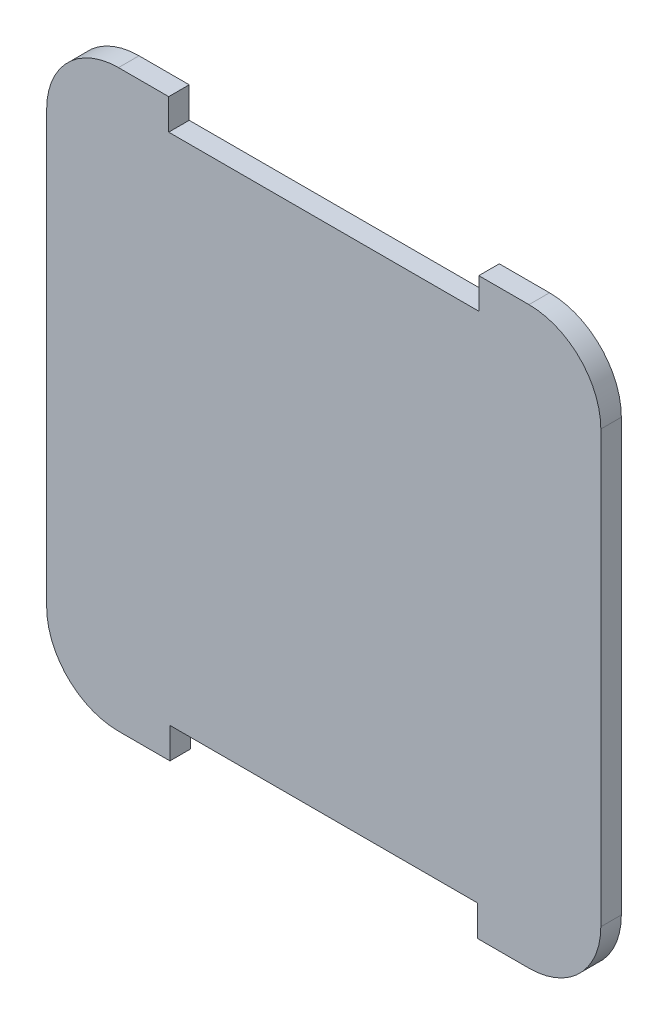
SolidWorks part; units mm, degrees
ref_plane "Front Plane" through (0, 0, 0) normal (0, 0, 1) x (1, 0, 0)
ref_plane "Top Plane" through (0, 0, 0) normal (0, 1, 0) x (1, 0, 0)
ref_plane "Right Plane" through (0, 0, 0) normal (1, 0, 0) x (0, 0, -1)
sketch "Sketch1" plane through (0, 0, 0) normal (0, 0, 1) x (1, 0, 0)
  line L2 (-13.5, 10.5) -> (-13.5, -10.5) construction
  line L5 (-13.5, 10.5) -> (-13.5, -10.5)
  line L6 (-10, 14) -> (10, 14)
  line L8 (-10, -14) -> (10, -14)
  line L9 (13.5, 10.5) -> (13.5, -10.5) construction
  line L10 (13.5, 10.5) -> (13.5, -10.5)
  arc A3 (-10, 14) -> (-13.5, 10.5) centre (-10, 10.5) ccw construction
  arc A7 (-10, 14) -> (-13.5, 10.5) centre (-10, 10.5) ccw
  arc A8 (10, -14) -> (13.5, -10.5) centre (10, -10.5) ccw construction
  arc A9 (-13.5, -10.5) -> (-10, -14) centre (-10, -10.5) ccw construction
  arc A10 (10, -14) -> (13.5, -10.5) centre (10, -10.5) ccw
  arc A11 (-13.5, -10.5) -> (-10, -14) centre (-10, -10.5) ccw
  arc A12 (13.5, 10.5) -> (10, 14) centre (10, 10.5) ccw construction
  arc A13 (13.5, 10.5) -> (10, 14) centre (10, 10.5) ccw
extrude "Boss-Extrude1" add sketch "Sketch1" along normal blind 1
sketch "Sketch2" plane through (0, 0, 1) normal (0, 0, 1) x (1, 0, 0)
  line L0 (10, 14) -> (-10, 14) construction
  line L1 (7.5538, 14) -> (-7.5538, 14)
  line L2 (7.2538, 12.5) -> (-7.2538, 12.5) construction
  line L3 (7.5538, 12.5) -> (-7.5538, 12.5)
  line L4 (-7.5538, 14) -> (-7.5538, 12.5) construction
  line L5 (-7.5538, 14) -> (-7.5538, 12.5)
  line L6 (7.5538, 12.5) -> (7.5538, 14) construction
  line L7 (7.5538, 12.5) -> (7.5538, 14)
  line L12 (-10, -14) -> (10, -14) construction
  line L13 (-7.4932, -14) -> (7.4932, -14)
  line L15 (-7.4964, -12.5) -> (7.4964, -12.5)
  line L16 (-7.4932, -14) -> (-7.4966, -12.446) construction
  line L17 (-7.4932, -14) -> (-7.4964, -12.5)
  line L18 (7.4932, -14) -> (7.4966, -12.446) construction
  line L19 (7.4932, -14) -> (7.4964, -12.5)
extrude "Cut-Extrude1" cut sketch "Sketch2" against normal up to next
